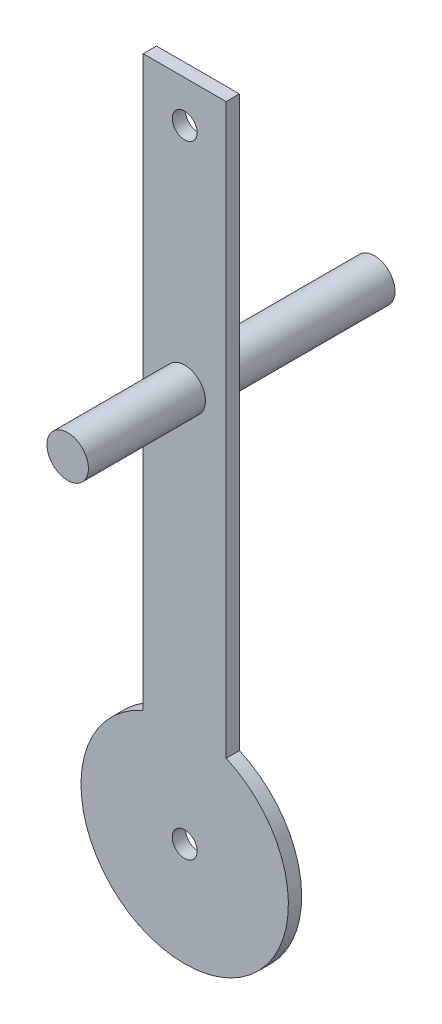
SolidWorks part; units mm, degrees
material "Cast Alloy Steel"
ref_plane "Front Plane" through (0, 0, 0) normal (0, 0, 1) x (1, 0, 0)
ref_plane "Top Plane" through (0, 0, 0) normal (0, 1, 0) x (1, 0, 0)
ref_plane "Right Plane" through (0, 0, 0) normal (1, 0, 0) x (0, 0, -1)
sketch "Sketch1" plane through (0, 0, 0) normal (0, 0, 1) x (1, 0, 0)
  line L0 (5, -1.4564) -> (5, -21.4564) construction
  line L2 (0, 0) -> (0, 68.5436)
  line L3 (0, 68.5436) -> (10, 68.5436)
  line L4 (10, 0) -> (10, 68.5436)
  arc A0 (0, 0) -> (10, 0) centre (5, -11.4564) ccw
  circle A1 centre (5, -11.4564) radius 1.5
  circle A2 centre (5, -1.4564) radius 1.5 construction
  circle A3 centre (5, -21.4564) radius 1.5 construction
  dimension "D3" = 25
  dimension "D5" = 3
  dimension "D6" = 3
  dimension "D1" = 10
  dimension "D2" = 5
  dimension "D4" = 80
  dimension "D7" = 20
extrude "Boss-Extrude1" add sketch "Sketch1" along normal blind 1.6
sketch "Sketch2" plane through (0, 0, 1.6) normal (0, 0, 1) x (1, 0, 0)
  line L1 (10, 68.5436) -> (0, 68.5436) construction
  circle A1 centre (5, 63.5436) radius 1.5
  point P7 (5, 68.5436)
  dimension "D1" = 3
  dimension "D3" = 5
extrude "Cut-Extrude1" cut sketch "Sketch2" against normal through all
sketch "Sketch3" plane through (0, 0, 1.6) normal (0, 0, 1) x (1, 0, 0)
  line L0 (10, 68.5436) -> (0, 68.5436) construction
  line L1 (0, 68.5436) -> (0, 0) construction
  circle A0 centre (5, 36.0436) radius 2.5
  dimension "D2" = 5
  dimension "D3" = 5
  dimension "D1" = 32.5
extrude "Boss-Extrude2" add sketch "Sketch3" along normal blind 14.1
sketch "Sketch4" plane through (0, 0, 0) normal (0, 0, -1) x (-1, 0, 0)
  line L0 (0, 68.5436) -> (0, 0) construction
  line L1 (-10, 68.5436) -> (0, 68.5436) construction
  circle A0 centre (-5, 36.0436) radius 2.5
  dimension "D2" = 5
  dimension "D1" = 5
  dimension "D3" = 32.5
extrude "Boss-Extrude3" add sketch "Sketch4" along normal blind 21.25
